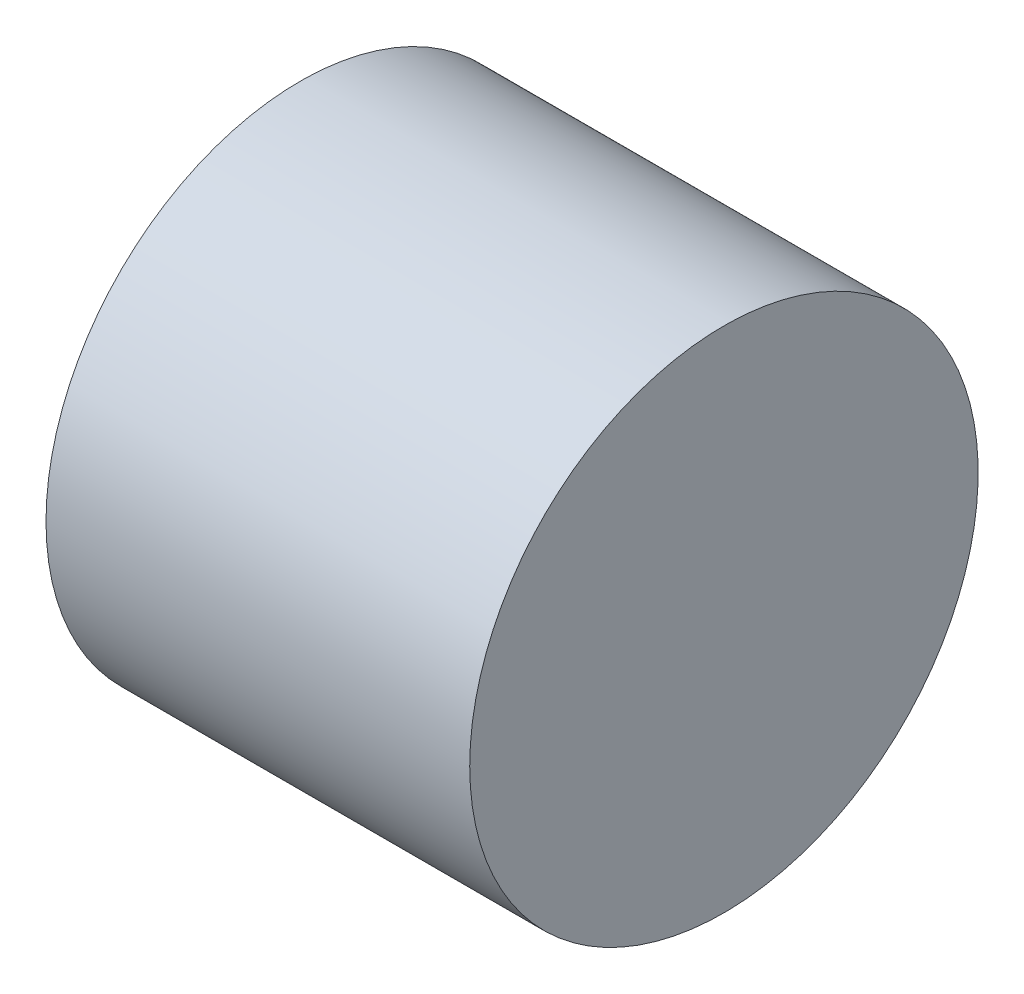
SolidWorks part; units mm, degrees
ref_plane "Front Plane" through (0, 0, 0) normal (0, 0, 1) x (1, 0, 0)
ref_plane "Top Plane" through (0, 0, 0) normal (0, 1, 0) x (1, 0, 0)
ref_plane "Right Plane" through (0, 0, 0) normal (1, 0, 0) x (0, 0, -1)
sketch "Croquis1" plane through (0, 0, 0) normal (0, 1, 0) x (1, 0, 0)
  line L0 (-5.1797, 0) -> (13.9741, 0) construction
  line L1 (-2.5, 0) -> (-2.5, 3)
  line L2 (-2.5, 3) -> (2.5, 3)
  line L3 (2.5, 3) -> (2.5, 0)
  line L4 (-2.5, 0) -> (2.5, 0)
  point P5 (0, 3)
  dimension "D1" = 3
  dimension "D2" = 5
revolve "Revolución1" add sketch "Croquis1" angle 360 about L0
